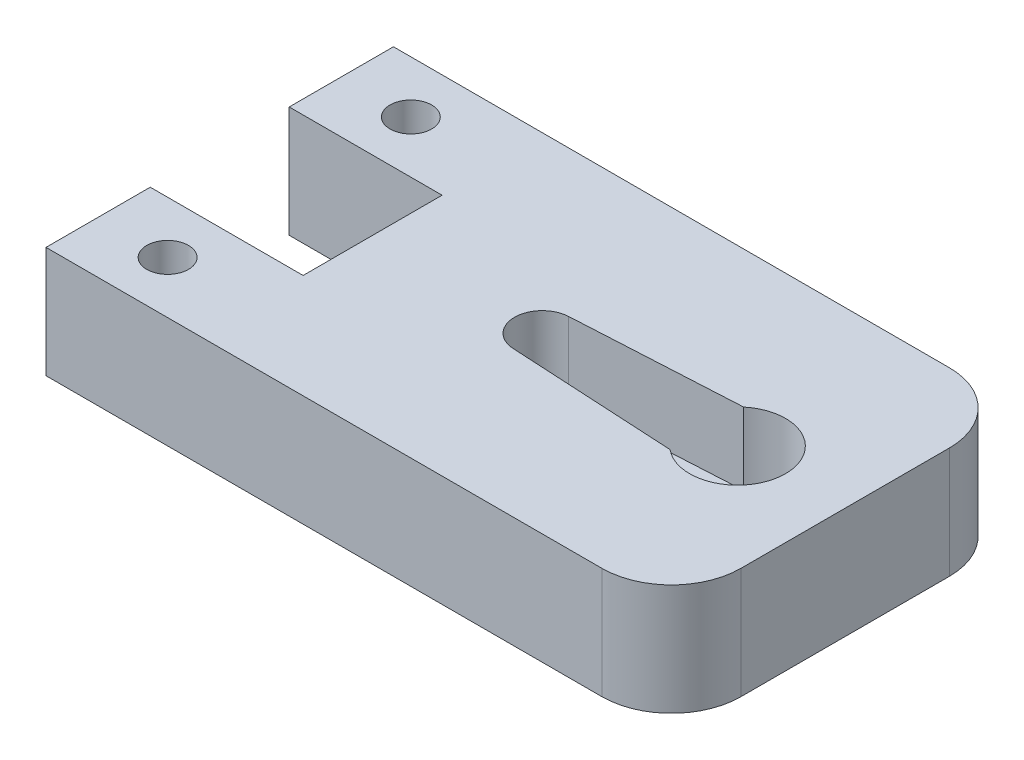
SolidWorks part; units mm, degrees
ref_plane "Front Plane" through (0, 0, 0) normal (0, 0, 1) x (1, 0, 0)
ref_plane "Top Plane" through (0, 0, 0) normal (0, 1, 0) x (1, 0, 0)
ref_plane "Right Plane" through (0, 0, 0) normal (1, 0, 0) x (0, 0, -1)
sketch "Sketch1" plane through (0, 0, 0) normal (0, 1, 0) x (1, 0, 0)
  line L0 (0, 12.5) -> (45, 12.5) construction
  line L1 (5, 0) -> (40, 0)
  line L2 (0, 5) -> (0, 20)
  line L3 (5, 25) -> (40, 25)
  line L4 (45, 5) -> (45, 20)
  line L5 (5, 25) -> (0, 25)
  line L6 (0, 25) -> (0, 20)
  line L7 (0, 5) -> (0, 0)
  line L8 (0, 0) -> (5, 0)
  arc A2 (45, 20) -> (40, 25) centre (40, 20) ccw
  arc A3 (40, 0) -> (45, 5) centre (40, 5) ccw
  point P9 (45, 25)
  point P13 (45, 0)
  point P16 (0, 0)
  point P19 (0, 25)
  dimension "D3" = 5
  dimension "D1" = 45
  dimension "D2" = 25
extrude "Boss-Extrude1" add sketch "Sketch1" along normal blind 8
sketch "Sketch2" plane through (0, 8, 0) normal (0, 1, 0) x (1, 0, 0)
  line L0 (0, 12.5) -> (45, 12.5) construction
  line L1 (0, 25) -> (0, 0) construction
  line L2 (45, 5) -> (45, 20) construction
  line L13 (35.0509, 15.15) -> (23.1009, 14.497)
  line L14 (35.0509, 9.85) -> (23.1009, 10.503)
  arc A4 (35.0509, 9.85) -> (35.0509, 15.15) centre (37.26, 12.5) ccw
  arc A5 (23.1009, 14.497) -> (23.1009, 10.503) centre (23.21, 12.5) ccw
  dimension "D1" = 6.9
  dimension "D2" = 7.74
  dimension "D3" = 4
  dimension "D4" = 5.3
  dimension "D5" = 14.05
  dimension "D6" = 11.95
extrude "Cut-Extrude1" cut sketch "Sketch2" against normal blind 5.2
sketch "Sketch3" plane through (0, 2.8, 0) normal (0, 1, 0) x (1, 0, 0)
  line L0 (0, 12.5) -> (45, 12.5) construction
  line L1 (0, 25) -> (0, 0) construction
  line L2 (45, 5) -> (45, 20) construction
  circle A2 centre (37.26, 12.5) radius 2.3
  dimension "D1" = 4.6
extrude "Boss-Extrude2" add sketch "Sketch3" along normal blind 1
sketch "Sketch4" plane through (0, 3.8, 0) normal (0, 1, 0) x (1, 0, 0)
  circle A2 centre (37.26, 12.5) radius 1.25
  dimension "D1" = 2.5
extrude "Cut-Extrude2" cut sketch "Sketch4" against normal through all
sketch "Sketch5" plane through (0, 8, 0) normal (0, 1, 0) x (1, 0, 0)
  line L0 (0, 25) -> (0, 0) construction
  line L9 (0, 17.5) -> (11, 17.5)
  line L10 (0, 17.5) -> (0, 7.5)
  line L11 (0, 7.5) -> (11, 7.5)
  line L12 (11, 17.5) -> (11, 7.5)
  line L13 (40, 25) -> (0, 25) construction
  circle A0 centre (5, 21.25) radius 1.5
  circle A1 centre (5, 3.75) radius 1.5
  point P13 (5.5, 17.5)
  dimension "D1" = 3
  dimension "D2" = 3
  dimension "D6" = 3.75
  dimension "D7" = 5
  dimension "D8" = 5
  dimension "D9" = 3.75
  dimension "D3" = 11
  dimension "D4" = 10
  dimension "D5" = 7.5
extrude "Cut-Extrude3" cut sketch "Sketch5" against normal through all
sketch "Sketch7" plane through (0, 2.8, 0) normal (0, 1, 0) x (1, 0, 0)
  line L0 (11, 12.5) -> (45, 12.5) construction
  line L1 (11, 7.5) -> (11, 17.5) construction
  line L2 (45, 5) -> (45, 20) construction
  circle A1 centre (22.81, 12.5) radius 0.6
  circle A2 centre (37.26, 12.5) radius 1.25 construction
  dimension "D1" = 1.2
  dimension "D2" = 14.45
extrude "Boss-Extrude3" add sketch "Sketch7" along normal blind 1.2
